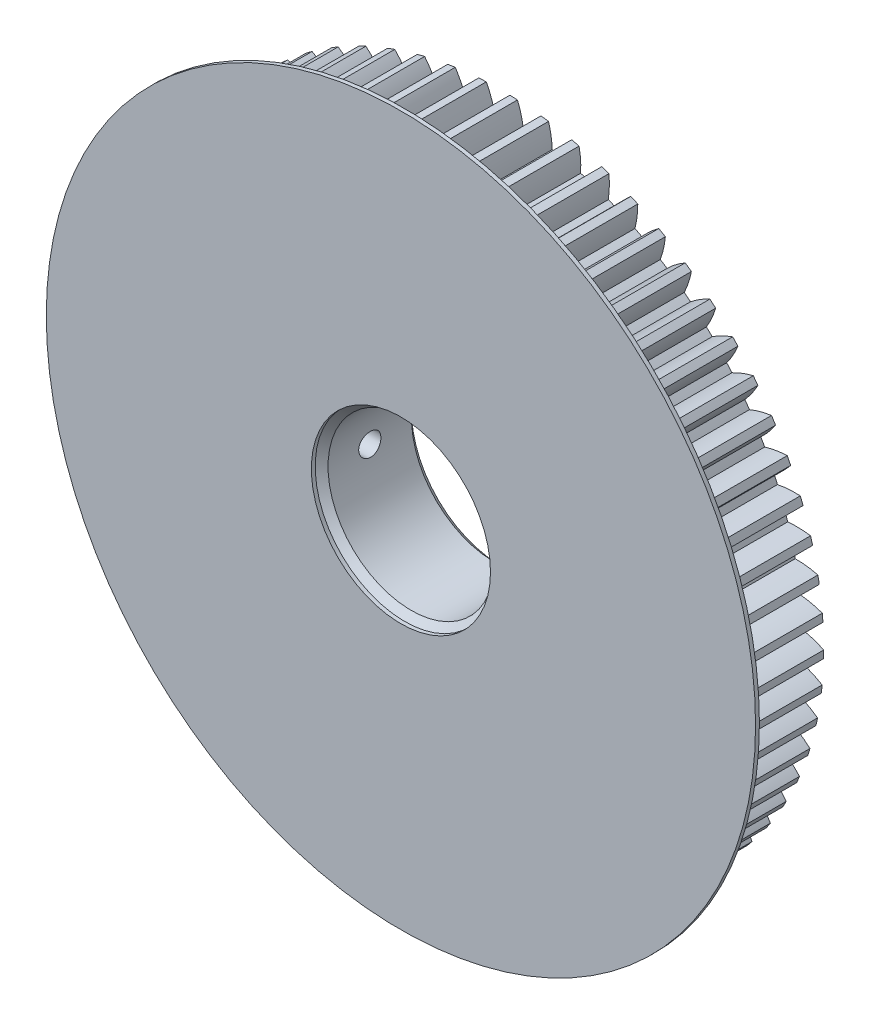
SolidWorks part; units mm, degrees
ref_plane "Front Plane" through (0, 0, 0) normal (0, 0, 1) x (1, 0, 0)
ref_plane "Top Plane" through (0, 0, 0) normal (0, 1, 0) x (1, 0, 0)
ref_plane "Right Plane" through (0, 0, 0) normal (1, 0, 0) x (0, 0, -1)
sketch "Sketch2" plane through (0, 0, 0) normal (0, 0, 1) x (1, 0, 0)
  circle A0 centre (0, 0) radius 50.25
  dimension "D1" = 100.5
extrude "gear outside diameter" add sketch "Sketch2" along normal blind 15
sketch "Sketch1" plane through (0, 0, 0) normal (0, 0, 1) x (1, 0, 0)
  line L0 (0, 45.81) -> (0, 0) construction
  line L1 (0, 0) -> (0.7266, 48.7446) construction
  line L2 (0, 0) -> (1.3709, 50.2313) construction
  line L3 (0, 0) -> (-0.1448, 15.635) construction
  line L4 (0, 45.81) -> (0, 46.875)
  line L5 (-0.8485, 45.8022) -> (-0.8682, 46.867)
  circle A0 centre (0, 0) radius 50.25 construction
  circle A1 centre (0, 0) radius 48.75 construction
  circle A2 centre (0, 0) radius 45.81 construction
  arc A3 (1.3709, 50.2313) -> (0, 45.81) centre (13.8613, 43.9354) ccw
  arc A4 (-2.301, 50.1973) -> (-0.8485, 45.8022) centre (-14.6727, 43.6711) cw
  arc A5 (-2.301, 50.1973) -> (1.3709, 50.2313) centre (0, 0) cw
  arc A6 (0, 46.875) -> (-0.8682, 46.867) centre (0, 0) ccw
  dimension "D1" = 100.5
  dimension "D2" = 97.5
  dimension "D3" = 91.62
  dimension "D7" = 93.75
  dimension "D4" = 1.385
  dimension "D5" = 0.854
  dimension "D6" = 1.563
extrude "gear tooth cut" cut sketch "Sketch1" along normal through all
pattern_circular "gear teeth" count 65 over 360 about axis through (0, 0, 0) along (0, 0, 1) of "gear tooth cut"
sketch "Sketch3" plane through (0, 0, 0) normal (0, 0, 1) x (1, 0, 0)
  circle A0 centre (0, 0) radius 46.875
  dimension "D1" = 93.75
extrude "gear dedendum circle" add sketch "Sketch3" along normal up to surface (15 mm away) up to face at (0, 0, 15)
sketch "Sketch4" plane through (0, 0, 15) normal (0, 0, 1) x (1, 0, 0)
  circle A0 centre (0, 0) radius 12.95
  dimension "D1" = 25.9
extrude "Cut-Extrude1" cut sketch "Sketch4" against normal through all
chamfer "Chamfer1" distance 1 angle 45 2 edges at (12.95, 0, 0) (12.95, 0, 15)
hole_wizard "#8-32 Tapped Hole1" positions "3DSketch1" profile "Sketch5" tap size "#8-32" standard "ANSI Inch"
sketch3d "3DSketch1"
  line L1 (-50.2431, -0.8332, 15) -> (-50.2431, -0.8332, 0)
  arc A2 (-33.2268, 37.6967, 15) -> (-34.1061, 36.903, 15) centre (0, 0, 15) ccw construction
  arc A3 (-33.2268, 37.6967, 0) -> (-34.1061, 36.903, 0) centre (0, 0, 0) ccw construction
  point P23 (0, 0, 65.25)
  point P27 (0, 0, 50.25)
  point P44 (-50.2431, -0.8332, 7.5)
sketch "Sketch5" plane through (-50.2431, -0.8332, 7.5) normal (0, 0, 1) x (0.0166, -0.9999, 0)
  line L0 (0, 0) -> (0, 37.3)
  line L1 (0, 37.3) -> (1.7272, 37.3)
  line L2 (1.7272, 37.3) -> (1.7272, 0)
  line L5 (1.7272, 0) -> (0, 0)
  line L11 (0, -6.35) -> (0, 107.95) construction
  dimension "Thru Tap Drill Dia." = 3.4544
  dimension "Thru Tap Drill Depth" = 37.3
sketch "Sketch6" plane through (0, 0, 15) normal (0, 0, 1) x (1, 0, 0)
  circle A0 centre (0, 0) radius 55.2341
  circle A1 centre (0, 0) radius 13.95 construction
  circle A2 centre (0, 0) radius 13.95
  point P0 (-2.0152, 55.1973)
  dimension "D1" = 5
extrude "Boss-Extrude1" add sketch "Sketch6" along normal blind 0.6
equation "\"N\"= 65'Number of teeth"
equation "\"m\"= 1.5'module  (using 25.4/P for imperial gears)"
equation "\"F\"= 15'face width"
equation "\"phi\"=20 'pressure angle"
equation "\"d\"=\"N\"*\"m\""
equation "\"OD\"=(\"N\"+2)*\"m\""
equation "\"db\"=\"d\"* cos( \"phi\" ) "
equation "\"D5@Sketch1\"= (tan( \"phi\" )-\"phi\" * pi /180)*180/ pi "
equation "\"D2@Sketch1\" = \"d\""
equation "\"D3@Sketch1\"=\"db\""
equation "\"D1@Sketch1\"=\"OD\""
equation "\"phiB\"= arccos( \"db\"/\"OD\" ) "
equation "\"D6@Sketch1\"=tan(\"phiB\")*180 /  pi -\"phiB\""
equation "\"D4@Sketch1\" = 360/\"N\"/4"
equation "\"D1@Sketch2\" = \"OD\""
equation "\"D1@gear teeth\"=\"N\""
equation "\"x\"=2.5-\"N\"*(1-cos(\"phi\"))"
equation "\"D1@Sketch3\" = (\"N\"-2.5)*\"m\""
equation "\"D7@Sketch1\" = (\"N\"-2.5)*\"m\""
equation "\"D1@gear outside diameter\" = \"F\""
